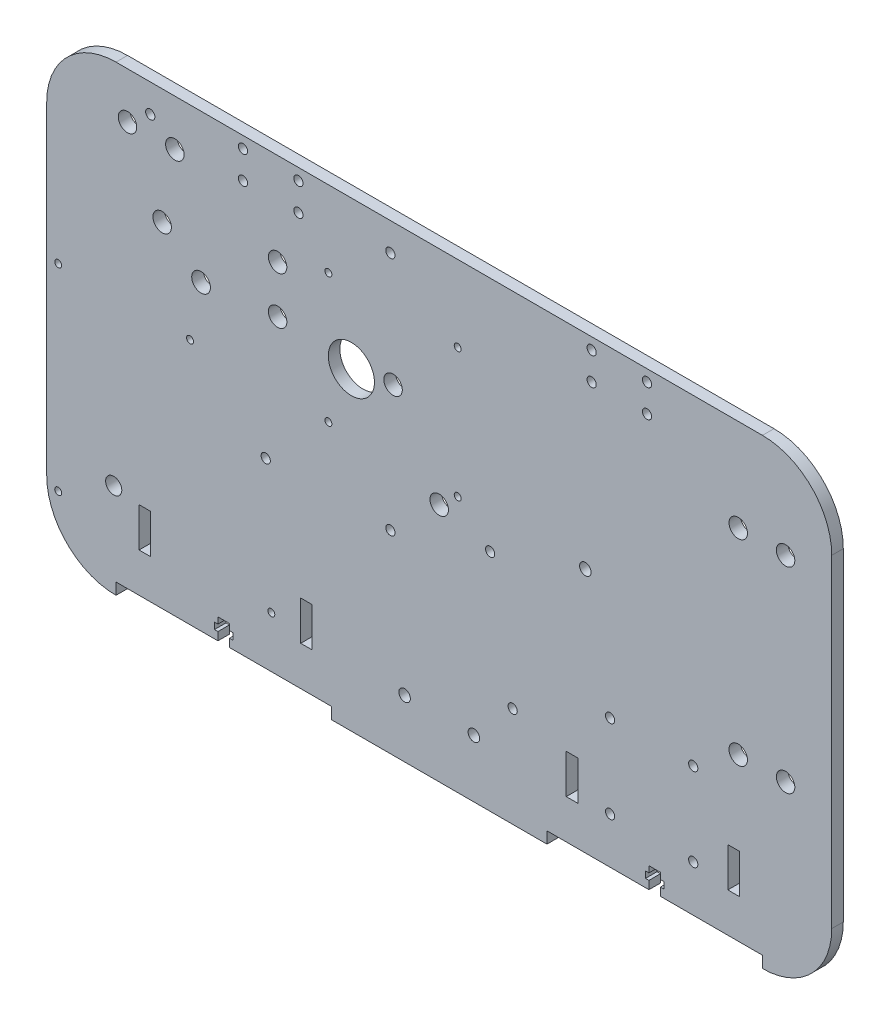
SolidWorks part; units mm, degrees
ref_plane "Alzado" through (0, 0, 0) normal (0, 0, 1) x (1, 0, 0)
ref_plane "Planta" through (0, 0, 0) normal (0, 1, 0) x (1, 0, 0)
ref_plane "Vista lateral" through (0, 0, 0) normal (1, 0, 0) x (0, 0, -1)
sketch "Croquis1" plane through (0, 0, 0) normal (0, 0, 1) x (1, 0, 0)
  line L1 (30, 0) -> (310, 0)
  line L2 (0, 30) -> (0, 170)
  line L3 (30, 200) -> (310, 200)
  line L4 (340, 30) -> (340, 170)
  arc A0 (30, 0) -> (0, 30) centre (30, 30) cw
  arc A1 (310, 0) -> (340, 30) centre (310, 30) ccw
  arc A2 (310, 200) -> (340, 170) centre (310, 170) cw
  arc A3 (0, 170) -> (30, 200) centre (30, 170) cw
  point P7 (0, 0)
  point P12 (340, 200)
  point P15 (0, 200)
  dimension "D3" = 30
  dimension "D1" = 200
  dimension "D2" = 340
extrude "Saliente-Extruir1" add sketch "Croquis1" along normal blind 5
sketch "Croquis2" plane through (0, 0, 5) normal (0, 0, -1) x (-1, 0, 0)
  line L0 (-55.5, 180) -> (-35, 180) construction
  line L2 (-310, 200) -> (-30, 200) construction
  line L3 (0, 170) -> (0, 30) construction
  line L4 (-100, 160) -> (-100, 139.5) construction
  line L5 (-310, 200) -> (-30, 200) construction
  line L6 (-299.5, 160) -> (-320, 160) construction
  line L7 (-340, 30) -> (-340, 170) construction
  line L8 (-320, 75) -> (-299.5, 75) construction
  line L9 (-30, 0) -> (-310, 0) construction
  line L10 (-100, 149.75) -> (-146.5265, 149.75) construction
  circle A0 centre (-55.5, 180) radius 4
  circle A1 centre (-35, 180) radius 4
  circle A2 centre (-100, 160) radius 4
  circle A3 centre (-100, 139.5) radius 4
  circle A4 centre (-299.5, 160) radius 4
  circle A5 centre (-320, 160) radius 4
  circle A6 centre (-320, 75) radius 4
  circle A7 centre (-299.5, 75) radius 4
  circle A8 centre (-150, 139) radius 4
  circle A9 centre (-170, 104) radius 4
  circle A10 centre (-50, 150) radius 4
  dimension "D1" = 8
  dimension "D10" = 40
  dimension "D14" = 8
  dimension "D19" = 8
  dimension "D2" = 20.5
  dimension "D3" = 35
  dimension "D4" = 20
  dimension "D5" = 20.5
  dimension "D6" = 40
  dimension "D7" = 100
  dimension "D8" = 20.5
  dimension "D9" = 20
  dimension "D11" = 20.5
  dimension "D12" = 20
  dimension "D13" = 75
  dimension "D15" = 150
  dimension "D16" = 61
  dimension "D17" = 35
  dimension "D18" = 20
  dimension "D20" = 50
  dimension "D21" = 50
extrude "Cortar-Extruir4" cut sketch "Croquis2" along normal blind 10
sketch "Croquis3" plane through (0, 0, 0) normal (0, 0, -1) x (-1, 0, 0)
  line L0 (-44.85, 187.84) -> (-148.85, 187.84) construction
  line L1 (-148.85, 187.84) -> (-148.85, 83.84) construction
  line L2 (-148.85, 83.84) -> (-94.85, 83.84) construction
  line L3 (-94.85, 83.84) -> (-44.85, 187.84) construction
  line L4 (-310, 200) -> (-30, 200) construction
  line L5 (0, 170) -> (0, 30) construction
  circle A0 centre (-148.85, 83.84) radius 2
  circle A1 centre (-94.85, 83.84) radius 2
  circle A2 centre (-44.85, 187.84) radius 2
  circle A3 centre (-148.85, 187.84) radius 2
  circle A4 centre (-131.95, 135.84) radius 10
  circle A5 centre (-66.85, 135.84) radius 4.05
  dimension "D1" = 4
  dimension "D5" = 20
  dimension "D6" = 8.1
  dimension "D2" = 104
  dimension "D3" = 104
  dimension "D4" = 54
  dimension "D7" = 16.9
  dimension "D8" = 52
  dimension "D9" = 52
  dimension "D10" = 82
  dimension "D11" = 12.16
  dimension "D12" = 66.85
extrude "Cortar-Extruir5" cut sketch "Croquis3" against normal blind 10
sketch "Croquis5" plane through (0, 0, 0) normal (0, 0, -1) x (-1, 0, 0)
  line L0 (-178, 167) -> (-122, 167) construction
  line L1 (-122, 167) -> (-122, 111) construction
  line L2 (-178, 167) -> (-178, 111) construction
  line L3 (-178, 111) -> (-122, 111) construction
  line L4 (-310, 200) -> (-30, 200) construction
  line L7 (0, 170) -> (0, 30) construction
  circle A0 centre (-178, 167) radius 1.5
  circle A1 centre (-122, 111) radius 1.5
  circle A2 centre (-122, 167) radius 1.5
  circle A3 centre (-178, 111) radius 1.5
  dimension "D1" = 3
  dimension "D4" = 3
  dimension "D2" = 56
  dimension "D3" = 56
  dimension "D5" = 33
  dimension "D6" = 122
extrude "Cortar-Extruir6" cut sketch "Croquis5" against normal blind 10
sketch "Croquis6" plane through (0, 0, 5) normal (0, 0, 1) x (1, 0, 0)
  line L0 (244, 61) -> (280, 61) construction
  line L1 (244, 61) -> (244, 25) construction
  line L2 (244, 25) -> (280, 25) construction
  line L3 (280, 25) -> (280, 61) construction
  line L4 (340, 30) -> (340, 170) construction
  line L5 (30, 0) -> (310, 0) construction
  circle A0 centre (244, 61) radius 2
  circle A1 centre (280, 61) radius 2
  circle A2 centre (244, 25) radius 2
  circle A3 centre (280, 25) radius 2
  dimension "D1" = 4
  dimension "D2" = 36
  dimension "D3" = 36
  dimension "D4" = 60
  dimension "D5" = 25
extrude "Cortar-Extruir7" cut sketch "Croquis6" against normal blind 10
sketch "Croquis7" plane through (0, 0, 5) normal (0, 0, 1) x (1, 0, 0)
  line L4 (30, 0) -> (310, 0)
  line L5 (340, 30) -> (340, 170)
  line L6 (310, 200) -> (30, 200)
  line L7 (0, 170) -> (0, 30)
  line L8 (30, 0) -> (310, 0)
  line L9 (340, 30) -> (340, 170)
  line L10 (310, 200) -> (30, 200)
  line L11 (0, 170) -> (0, 30)
  circle A0 centre (50, 150) radius 4 construction
  circle A1 centre (100, 160) radius 4 construction
  circle A2 centre (100, 139.5) radius 4 construction
  circle A3 centre (299.5, 75) radius 4 construction
  arc A4 (0, 30) -> (30, 0) centre (30, 30) ccw
  arc A5 (310, 0) -> (340, 30) centre (310, 30) ccw
  arc A6 (340, 170) -> (310, 200) centre (310, 170) ccw
  arc A7 (30, 200) -> (0, 170) centre (30, 170) ccw
  arc A8 (0, 30) -> (30, 0) centre (30, 30) ccw
  arc A9 (310, 0) -> (340, 30) centre (310, 30) ccw
  arc A10 (340, 170) -> (310, 200) centre (310, 170) ccw
  arc A11 (30, 200) -> (0, 170) centre (30, 170) ccw
  circle A12 centre (320, 75) radius 4 construction
  circle A13 centre (299.5, 160) radius 4 construction
  circle A14 centre (320, 160) radius 4 construction
  circle A15 centre (55.5, 180) radius 4 construction
  circle A16 centre (35, 180) radius 4 construction
  circle A17 centre (50, 150) radius 4
  circle A18 centre (100, 160) radius 4
  circle A19 centre (100, 139.5) radius 4
  circle A20 centre (299.5, 75) radius 4
  circle A21 centre (320, 75) radius 4
  circle A22 centre (299.5, 160) radius 4
  circle A23 centre (320, 160) radius 4
  circle A24 centre (55.5, 180) radius 4
  circle A25 centre (35, 180) radius 4
  dimension "D1" = 0
sketch "Croquis8" plane through (0, 0, 5) normal (0, 0, 1) x (1, 0, 0)
  line L0 (236, 195) -> (236, 183) construction
  line L1 (236, 195) -> (260, 195) construction
  line L2 (236, 183) -> (260, 183) construction
  line L3 (260, 183) -> (260, 195) construction
  line L4 (85, 195) -> (85, 183) construction
  line L5 (85, 195) -> (109, 195) construction
  line L6 (85, 183) -> (109, 183) construction
  line L7 (109, 183) -> (109, 195) construction
  line L8 (310, 200) -> (30, 200) construction
  line L9 (340, 30) -> (340, 170) construction
  line L10 (0, 170) -> (0, 30) construction
  circle A0 centre (236, 195) radius 2
  circle A1 centre (236, 183) radius 2
  circle A2 centre (260, 183) radius 2
  circle A3 centre (260, 195) radius 2
  circle A4 centre (85, 195) radius 2
  circle A5 centre (85, 183) radius 2
  circle A6 centre (109, 183) radius 2
  circle A7 centre (109, 195) radius 2
  dimension "D1" = 24
  dimension "D2" = 12
  dimension "D3" = 24
  dimension "D4" = 12
  dimension "D5" = 5
  dimension "D6" = 80
  dimension "D7" = 85
extrude "Cortar-Extruir8" cut sketch "Croquis8" against normal blind 10
sketch "Croquis9" plane through (0, 0, 0) normal (0, 0, -1) x (-1, 0, 0)
  line L0 (-233.2967, 111.4949) -> (-201.8, 43.4) construction
  line L1 (-201.8, 43.4) -> (-192.05, 97.4132) construction
  line L2 (-192.05, 97.4132) -> (-233.2967, 111.4949) construction
  line L3 (-62.0804, 111.91) -> (-4.98, 111.91) construction
  line L4 (-4.98, 111.91) -> (-4.98, 26.56) construction
  line L5 (-4.98, 26.56) -> (-97.2809, 27.16) construction
  line L6 (-62.0804, 111.91) -> (-97.2809, 27.16) construction
  line L8 (-30, 0) -> (-310, 0) construction
  line L9 (0, 170) -> (0, 30) construction
  line L10 (-340, 30) -> (-340, 170) construction
  circle A0 centre (-29.01, 40.6565) radius 3.5
  circle A1 centre (-62.0804, 111.91) radius 1.5
  circle A2 centre (-4.98, 111.91) radius 1.5
  circle A3 centre (-97.2809, 27.16) radius 1.5
  circle A4 centre (-4.98, 26.56) radius 1.5
  circle A5 centre (-233.2967, 111.4949) radius 2.5
  circle A6 centre (-201.8, 43.4) radius 2
  circle A7 centre (-192.05, 97.4132) radius 2
  dimension "D1" = 24.03
  dimension "D2" = 13.94
  dimension "D3" = 26.56
  dimension "D4" = 4.98
  dimension "D5" = 54.8862
  dimension "D6" = 43.5843
  dimension "D7" = 75.0264
  dimension "D8" = 43.4
  dimension "D9" = 138.2
extrude "Cortar-Extruir9" cut sketch "Croquis9" against normal blind 10
sketch "Croquis10" plane through (0, 0, 5) normal (0, 0, 1) x (1, 0, 0)
  line L0 (123.3333, 5) -> (123.3333, 0)
  line L1 (30, 0) -> (310, 0)
  line L2 (30, 0) -> (30, 5)
  line L3 (30, 5) -> (310, 5)
  line L4 (310, 0) -> (310, 5)
  line L5 (216.6667, 5) -> (216.6667, 0)
  point P10 (30, 2.5)
  line M48 (30, 0) -> (310, 0)
  dimension "D1" = 93.3333
  dimension "D2" = 93.3333
  dimension "D3" = 5
extrude "Cortar-Extruir10" cut sketch "Croquis10" against normal blind 10 contours L3 L2 L0 M48 | L3 L5 L1 L4
sketch "Croquis12" plane through (0, 0, 5) normal (0, 0, 1) x (1, 0, 0)
  line L0 (76.6667, 5) -> (76.6667, 14) construction
  line L1 (30, 5) -> (123.3333, 5) construction
  line L2 (170, 0) -> (170, 18.6393) construction
  line L3 (123.3333, 0) -> (216.6667, 0) construction
  line L4 (74.1667, 5) -> (74.1667, 8.5)
  line L5 (74.1667, 8.5) -> (72.6667, 8.5)
  line L6 (72.6667, 8.5) -> (72.6667, 11.3)
  line L7 (72.6667, 11.3) -> (74.1667, 11.3)
  line L8 (74.1667, 11.3) -> (74.1667, 14)
  line L9 (74.1667, 14) -> (79.1667, 14)
  line L10 (79.1667, 8.5) -> (80.6667, 8.5)
  line L11 (79.1667, 5) -> (79.1667, 8.5)
  line L12 (80.6667, 8.5) -> (80.6667, 11.3)
  line L13 (80.6667, 11.3) -> (79.1667, 11.3)
  line L14 (79.1667, 11.3) -> (79.1667, 14)
  line L15 (263.3333, 5) -> (263.3333, 14) construction
  line L16 (260.8333, 11.3) -> (260.8333, 14)
  line L17 (259.3333, 11.3) -> (260.8333, 11.3)
  line L18 (259.3333, 8.5) -> (259.3333, 11.3)
  line L19 (260.8333, 5) -> (260.8333, 8.5)
  line L20 (260.8333, 8.5) -> (259.3333, 8.5)
  line L21 (265.8333, 14) -> (260.8333, 14)
  line L22 (265.8333, 11.3) -> (265.8333, 14)
  line L23 (267.3333, 11.3) -> (265.8333, 11.3)
  line L24 (267.3333, 8.5) -> (267.3333, 11.3)
  line L25 (265.8333, 8.5) -> (267.3333, 8.5)
  line L26 (265.8333, 5) -> (265.8333, 8.5)
  line L27 (74.1667, 5) -> (79.1667, 5)
  line L28 (260.8333, 5) -> (265.8333, 5)
  point P1 (76.6667, 14)
  dimension "D1" = 2.8
  dimension "D2" = 4
  dimension "D3" = 9
  dimension "D4" = 3.5
  dimension "D5" = 2.5
extrude "Cortar-Extruir14" cut sketch "Croquis12" against normal blind 5
sketch "Croquis13" plane through (0, 0, 5) normal (0, 0, 1) x (1, 0, 0)
  line L0 (170, 0) -> (170, 28.0268) construction
  line L1 (123.3333, 0) -> (216.6667, 0) construction
  line L2 (79.1667, 5) -> (123.3333, 5) construction
  line L3 (110, 5) -> (115, 5)
  line L4 (110, 5) -> (110, 39)
  line L5 (110, 39) -> (115, 39)
  line L6 (115, 5) -> (115, 39)
  line L7 (225, 5) -> (225, 39)
  line L8 (230, 39) -> (225, 39)
  line L9 (230, 5) -> (230, 39)
  line L10 (230, 5) -> (225, 5)
  line L11 (110, 22) -> (115, 22)
  line L12 (225, 22) -> (230, 22)
  line L13 (30, 5) -> (74.1667, 5) construction
  line L14 (40, 5) -> (45, 5)
  line L15 (40, 5) -> (40, 39)
  line L16 (40, 39) -> (45, 39)
  line L17 (45, 5) -> (45, 39)
  line L18 (40, 22) -> (45, 22)
  line L19 (300, 22) -> (295, 22)
  line L20 (295, 5) -> (295, 39)
  line L21 (300, 39) -> (295, 39)
  line L22 (300, 5) -> (300, 39)
  line L23 (300, 5) -> (295, 5)
  dimension "D1" = 5
  dimension "D2" = 60
  dimension "D3" = 34
  dimension "D4" = 5
  dimension "D5" = 70
extrude "Cortar-Extruir15" cut sketch "Croquis13" against normal blind 5 contours L15 L18 L17 L16 | L4 L11 L6 L5 | L7 L12 L9 L8 | L19 L22 L21 L20
sketch "Croquis14" plane through (0, 0, 5) normal (0, 0, 1) x (1, 0, 0)
  line L0 (170, 0) -> (170, 25) construction
  line L1 (123.3333, 0) -> (216.6667, 0) construction
  line L2 (155, 25) -> (170, 25) construction
  line L3 (79.1667, 5) -> (123.3333, 5) construction
  circle A0 centre (155, 25) radius 2.5
  circle A1 centre (185, 25) radius 2.5
  dimension "D2" = 5
  dimension "D1" = 15
  dimension "D3" = 20
extrude "Cortar-Extruir16" cut sketch "Croquis14" against normal blind 10
sketch "Croquis15" plane through (0, 0, 5) normal (0, 0, 1) x (1, 0, 0)
  line L0 (300, 39) -> (295, 39) construction
  line L1 (300, 22) -> (300, 39) construction
  line L2 (295, 22) -> (295, 39) construction
  line L3 (300, 22) -> (295, 22) construction
  line L4 (225, 22) -> (230, 22) construction
  line L5 (230, 39) -> (225, 39) construction
  line L6 (230, 22) -> (230, 39) construction
  line L7 (225, 22) -> (225, 39) construction
  line L8 (110, 39) -> (115, 39) construction
  line L9 (115, 22) -> (115, 39) construction
  line L10 (110, 22) -> (110, 39) construction
  line L11 (110, 22) -> (115, 22) construction
  line L12 (40, 22) -> (45, 22) construction
  line L13 (40, 39) -> (45, 39) construction
  line L14 (45, 22) -> (45, 39) construction
  line L15 (40, 22) -> (40, 39) construction
  line L16 (300, 39) -> (295, 39)
  line L17 (300, 22) -> (300, 39)
  line L18 (295, 22) -> (295, 39)
  line L19 (300, 22) -> (295, 22)
  line L20 (225, 22) -> (230, 22)
  line L21 (230, 39) -> (225, 39)
  line L22 (230, 22) -> (230, 39)
  line L23 (225, 22) -> (225, 39)
  line L24 (110, 39) -> (115, 39)
  line L25 (115, 22) -> (115, 39)
  line L26 (110, 22) -> (110, 39)
  line L27 (110, 22) -> (115, 22)
  line L28 (40, 22) -> (45, 22)
  line L29 (40, 39) -> (45, 39)
  line L30 (45, 22) -> (45, 39)
  line L31 (40, 22) -> (40, 39)
  line L34 (267.3333, 8.5) -> (265.8333, 8.5)
  line L35 (265.8333, 8.5) -> (265.8333, 5)
  line L36 (265.8333, 5) -> (310, 5)
  line L37 (310, 5) -> (310, 0)
  line L38 (340, 30) -> (340, 170)
  line L39 (310, 200) -> (30, 200)
  line L40 (0, 170) -> (0, 30)
  line L41 (30, 0) -> (30, 5)
  line L42 (30, 5) -> (74.1667, 5)
  line L43 (74.1667, 5) -> (74.1667, 8.5)
  line L44 (74.1667, 8.5) -> (72.6667, 8.5)
  line L45 (72.6667, 8.5) -> (72.6667, 11.3)
  line L46 (72.6667, 11.3) -> (74.1667, 11.3)
  line L47 (74.1667, 11.3) -> (74.1667, 14)
  line L48 (74.1667, 14) -> (79.1667, 14)
  line L49 (79.1667, 14) -> (79.1667, 11.3)
  line L50 (79.1667, 11.3) -> (80.6667, 11.3)
  line L51 (80.6667, 11.3) -> (80.6667, 8.5)
  line L52 (80.6667, 8.5) -> (79.1667, 8.5)
  line L53 (79.1667, 8.5) -> (79.1667, 5)
  line L54 (79.1667, 5) -> (123.3333, 5)
  line L55 (123.3333, 5) -> (123.3333, 0)
  line L56 (123.3333, 0) -> (216.6667, 0)
  line L57 (216.6667, 0) -> (216.6667, 5)
  line L58 (216.6667, 5) -> (260.8333, 5)
  line L59 (260.8333, 5) -> (260.8333, 8.5)
  line L60 (260.8333, 8.5) -> (259.3333, 8.5)
  line L61 (259.3333, 8.5) -> (259.3333, 11.3)
  line L62 (259.3333, 11.3) -> (260.8333, 11.3)
  line L63 (260.8333, 11.3) -> (260.8333, 14)
  line L64 (260.8333, 14) -> (265.8333, 14)
  line L65 (265.8333, 14) -> (265.8333, 11.3)
  line L66 (265.8333, 11.3) -> (267.3333, 11.3)
  line L67 (267.3333, 11.3) -> (267.3333, 8.5)
  line L68 (267.3333, 8.5) -> (265.8333, 8.5)
  line L69 (265.8333, 8.5) -> (265.8333, 5)
  line L70 (265.8333, 5) -> (310, 5)
  line L71 (310, 5) -> (310, 0)
  line L72 (340, 30) -> (340, 170)
  line L73 (310, 200) -> (30, 200)
  line L74 (0, 170) -> (0, 30)
  line L75 (30, 0) -> (30, 5)
  line L76 (30, 5) -> (74.1667, 5)
  line L77 (74.1667, 5) -> (74.1667, 8.5)
  line L78 (74.1667, 8.5) -> (72.6667, 8.5)
  line L79 (72.6667, 8.5) -> (72.6667, 11.3)
  line L80 (72.6667, 11.3) -> (74.1667, 11.3)
  line L81 (74.1667, 11.3) -> (74.1667, 14)
  line L82 (74.1667, 14) -> (79.1667, 14)
  line L83 (79.1667, 14) -> (79.1667, 11.3)
  line L84 (79.1667, 11.3) -> (80.6667, 11.3)
  line L85 (80.6667, 11.3) -> (80.6667, 8.5)
  line L86 (80.6667, 8.5) -> (79.1667, 8.5)
  line L87 (79.1667, 8.5) -> (79.1667, 5)
  line L88 (79.1667, 5) -> (123.3333, 5)
  line L89 (123.3333, 5) -> (123.3333, 0)
  line L90 (123.3333, 0) -> (216.6667, 0)
  line L91 (216.6667, 0) -> (216.6667, 5)
  line L92 (216.6667, 5) -> (260.8333, 5)
  line L93 (260.8333, 5) -> (260.8333, 8.5)
  line L94 (260.8333, 8.5) -> (259.3333, 8.5)
  line L95 (259.3333, 8.5) -> (259.3333, 11.3)
  line L96 (259.3333, 11.3) -> (260.8333, 11.3)
  line L97 (260.8333, 11.3) -> (260.8333, 14)
  line L98 (260.8333, 14) -> (265.8333, 14)
  line L99 (265.8333, 14) -> (265.8333, 11.3)
  line L100 (265.8333, 11.3) -> (267.3333, 11.3)
  line L101 (267.3333, 11.3) -> (267.3333, 8.5)
  circle A0 centre (201.8, 43.4) radius 2 construction
  circle A1 centre (185, 25) radius 2.5 construction
  circle A2 centre (155, 25) radius 2.5 construction
  circle A3 centre (244, 25) radius 2 construction
  arc A4 (310, 0) -> (340, 30) centre (310, 30) ccw
  arc A5 (340, 170) -> (310, 200) centre (310, 170) ccw
  arc A6 (30, 200) -> (0, 170) centre (30, 170) ccw
  arc A7 (0, 30) -> (30, 0) centre (30, 30) ccw
  arc A8 (310, 0) -> (340, 30) centre (310, 30) ccw
  arc A9 (340, 170) -> (310, 200) centre (310, 170) ccw
  arc A10 (30, 200) -> (0, 170) centre (30, 170) ccw
  arc A11 (0, 30) -> (30, 0) centre (30, 30) ccw
  circle A12 centre (280, 25) radius 2 construction
  circle A13 centre (280, 61) radius 2 construction
  circle A14 centre (299.5, 160) radius 4 construction
  circle A15 centre (320, 160) radius 4 construction
  circle A16 centre (320, 75) radius 4 construction
  circle A17 centre (299.5, 75) radius 4 construction
  circle A18 centre (244, 61) radius 2 construction
  circle A19 centre (192.05, 97.4132) radius 2 construction
  circle A20 centre (233.2967, 111.4949) radius 2.5 construction
  circle A21 centre (260, 183) radius 2 construction
  circle A22 centre (260, 195) radius 2 construction
  circle A23 centre (236, 195) radius 2 construction
  circle A24 centre (236, 183) radius 2 construction
  circle A25 centre (178, 167) radius 1.5 construction
  circle A26 centre (178, 111) radius 1.5 construction
  circle A27 centre (170, 104) radius 4 construction
  circle A28 centre (148.85, 83.84) radius 2 construction
  circle A29 centre (150, 139) radius 4 construction
  circle A30 centre (148.85, 187.84) radius 2 construction
  circle A31 centre (122, 167) radius 1.5 construction
  circle A32 centre (131.95, 135.84) radius 10 construction
  circle A33 centre (122, 111) radius 1.5 construction
  circle A34 centre (94.85, 83.84) radius 2 construction
  circle A35 centre (97.2809, 27.16) radius 1.5 construction
  circle A36 centre (4.98, 26.56) radius 1.5 construction
  circle A37 centre (29.01, 40.6565) radius 3.5 construction
  circle A38 centre (4.98, 111.91) radius 1.5 construction
  circle A39 centre (62.0804, 111.91) radius 1.5 construction
  circle A40 centre (66.85, 135.84) radius 4.05 construction
  circle A41 centre (100, 139.5) radius 4 construction
  circle A42 centre (100, 160) radius 4 construction
  circle A43 centre (109, 183) radius 2 construction
  circle A44 centre (109, 195) radius 2 construction
  circle A45 centre (85, 195) radius 2 construction
  circle A46 centre (85, 183) radius 2 construction
  circle A47 centre (50, 150) radius 4 construction
  circle A48 centre (44.85, 187.84) radius 2 construction
  circle A49 centre (55.5, 180) radius 4 construction
  circle A50 centre (35, 180) radius 4 construction
  circle A51 centre (201.8, 43.4) radius 2
  circle A52 centre (185, 25) radius 2.5
  circle A53 centre (155, 25) radius 2.5
  circle A54 centre (244, 25) radius 2
  circle A55 centre (280, 25) radius 2
  circle A56 centre (280, 61) radius 2
  circle A57 centre (299.5, 160) radius 4
  circle A58 centre (320, 160) radius 4
  circle A59 centre (320, 75) radius 4
  circle A60 centre (299.5, 75) radius 4
  circle A61 centre (244, 61) radius 2
  circle A62 centre (192.05, 97.4132) radius 2
  circle A63 centre (233.2967, 111.4949) radius 2.5
  circle A64 centre (260, 183) radius 2
  circle A65 centre (260, 195) radius 2
  circle A66 centre (236, 195) radius 2
  circle A67 centre (236, 183) radius 2
  circle A68 centre (178, 167) radius 1.5
  circle A69 centre (178, 111) radius 1.5
  circle A70 centre (170, 104) radius 4
  circle A71 centre (148.85, 83.84) radius 2
  circle A72 centre (150, 139) radius 4
  circle A73 centre (148.85, 187.84) radius 2
  circle A74 centre (122, 167) radius 1.5
  circle A75 centre (131.95, 135.84) radius 10
  circle A76 centre (122, 111) radius 1.5
  circle A77 centre (94.85, 83.84) radius 2
  circle A78 centre (97.2809, 27.16) radius 1.5
  circle A79 centre (4.98, 26.56) radius 1.5
  circle A80 centre (29.01, 40.6565) radius 3.5
  circle A81 centre (4.98, 111.91) radius 1.5
  circle A82 centre (62.0804, 111.91) radius 1.5
  circle A83 centre (66.85, 135.84) radius 4.05
  circle A84 centre (100, 139.5) radius 4
  circle A85 centre (100, 160) radius 4
  circle A86 centre (109, 183) radius 2
  circle A87 centre (109, 195) radius 2
  circle A88 centre (85, 195) radius 2
  circle A89 centre (85, 183) radius 2
  circle A90 centre (50, 150) radius 4
  circle A91 centre (44.85, 187.84) radius 2
  circle A92 centre (55.5, 180) radius 4
  circle A93 centre (35, 180) radius 4
  dimension "D1" = 0
